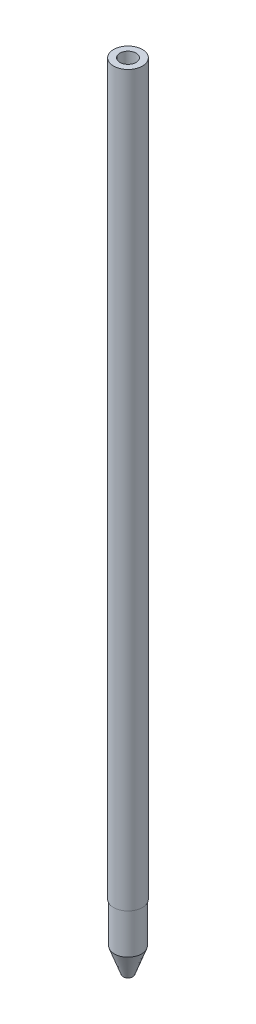
SolidWorks part; units mm, degrees
material "Custom Plastic"
ref_plane "Front Plane" through (0, 0, 0) normal (0, 0, 1) x (1, 0, 0)
ref_plane "Top Plane" through (0, 0, 0) normal (0, 1, 0) x (1, 0, 0)
ref_plane "Right Plane" through (0, 0, 0) normal (1, 0, 0) x (0, 0, -1)
other "Configuration Table"
sketch "Sketch2" plane through (0, 0, 0) normal (0, 1, 0) x (1, 0, 0)
  circle A0 centre (0, 0) radius 1.778
  dimension "D1" = 3.556
extrude "Boss-Extrude1" add sketch "Sketch2" along normal blind 89.9922
ref_plane "Plane1" through (0, 2.9972, 0) normal (0, 1, 0) x (1, 0, 0)
sketch "Sketch3" plane through (0, 2.9972, 0) normal (0, 1, 0) x (1, 0, 0)
  circle A0 centre (0, 0) radius 1.6891
  dimension "D1" = 3.3782
extrude "Boss-Extrude2" add sketch "Sketch3" against normal blind 8.001
sketch "Sketch4" plane through (0, 89.9922, 0) normal (0, 1, 0) x (1, 0, 0)
  circle A0 centre (0, 0) radius 0.9995
  dimension "D1" = 1.999
extrude "Cut-Extrude1" cut sketch "Sketch4" against normal blind 86.995
sketch "Sketch5" plane through (0, 2.9972, 0) normal (0, 1, 0) x (1, 0, 0)
  circle A0 centre (0, 0) radius 1.7526
  dimension "D1" = 3.5052
extrude "Cut-Extrude2" cut sketch "Sketch5" against normal up to surface (2.9972 mm away) up to face at (0, 0, 1.6891)
sketch "Sketch6" plane through (0, 0, 0) normal (0, 0, 1) x (1, 0, 0)
  line L0 (-1.6891, -5.0038) -> (-0.5982, -8.001)
  line L1 (-0.5982, -8.001) -> (0, -8.001)
  line L3 (-1.6891, -5.0038) -> (0, -5.0038)
  line L4 (0, 0) -> (0, -9.4977) construction
  line L5 (0, -5.0038) -> (0, -8.001)
  dimension "D1" = 2.9972
  dimension "D2" = 20
revolve "Revolve2" add sketch "Sketch6" angle 360 about L4
